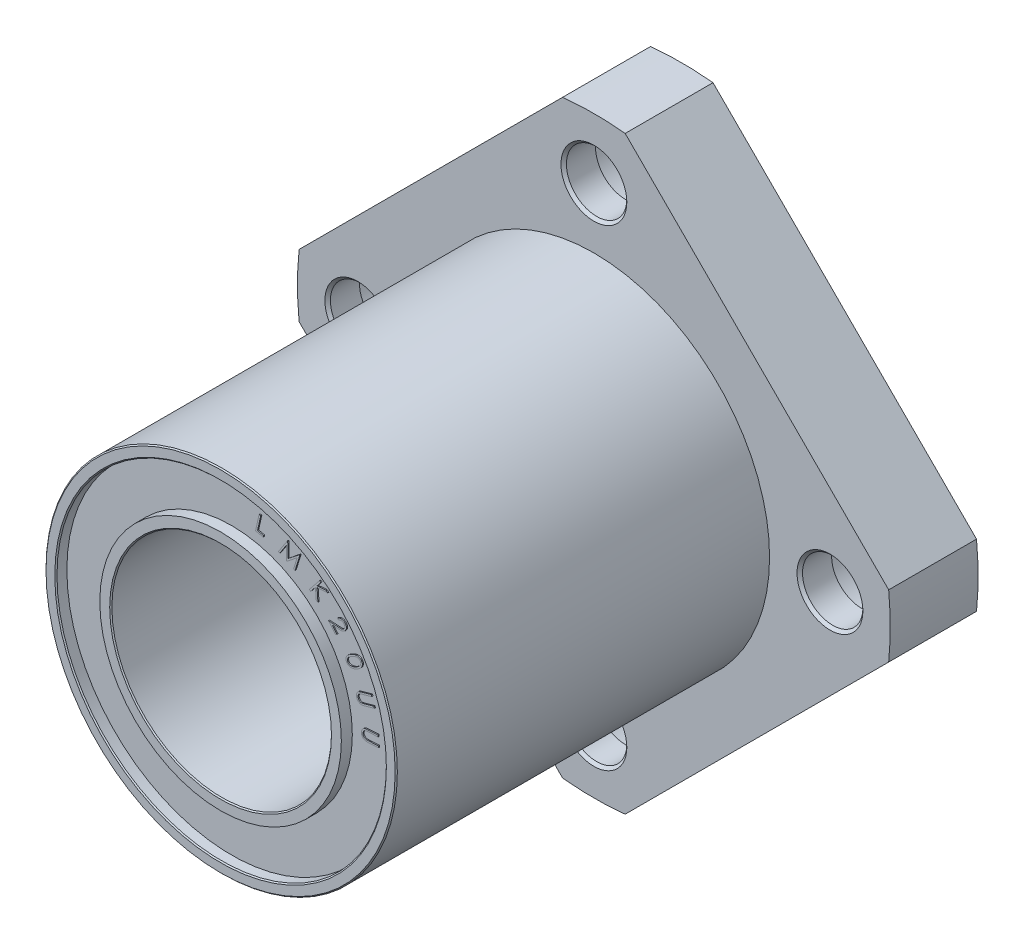
SolidWorks part; units mm, degrees
ref_plane "Front Plane" through (0, 0, 0) normal (0, 0, 1) x (1, 0, 0)
ref_plane "Top Plane" through (0, 0, 0) normal (0, 1, 0) x (1, 0, 0)
ref_plane "Right Plane" through (0, 0, 0) normal (1, 0, 0) x (0, 0, -1)
sketch "Sketch1" plane through (0, 0, 0) normal (0, 0, 1) x (1, 0, 0)
  line L1 (-2.8492, 26.8492) -> (-26.8492, 2.8492)
  line L2 (-26.8492, -2.8492) -> (-2.8492, -26.8492)
  line L3 (2.8492, -26.8492) -> (26.8492, -2.8492)
  line L4 (26.8492, 2.8492) -> (2.8492, 26.8492)
  arc A0 (-26.8492, 2.8492) -> (-26.8492, -2.8492) centre (0, 0) ccw
  circle A1 centre (0, 0) radius 21 construction
  arc A2 (-2.8492, -26.8492) -> (2.8492, -26.8492) centre (0, 0) ccw
  arc A3 (26.8492, -2.8492) -> (26.8492, 2.8492) centre (0, 0) ccw
  arc A4 (2.8492, 26.8492) -> (-2.8492, 26.8492) centre (0, 0) ccw
  dimension "D1" = 54
  dimension "D2" = 42
extrude "Boss-Extrude1" add sketch "Sketch1" along normal blind 8
sketch "Sketch2" plane through (0, 0, 8) normal (0, 0, 1) x (1, 0, 0)
  circle A0 centre (0, 0) radius 16
  dimension "D1" = 32
extrude "Boss-Extrude2" add sketch "Sketch2" along normal blind 34
sketch "Sketch3" plane through (0, 0, 0) normal (0, 0, -1) x (-1, 0, 0)
  circle A0 centre (0, 0) radius 21.5 construction
  circle A1 centre (0, 21.5) radius 4.5
  dimension "D1" = 43
  dimension "D2" = 9
extrude "Cut-Extrude1" cut sketch "Sketch3" against normal blind 5.1
sketch "Sketch4" plane through (0, 0, 5.1) normal (0, 0, -1) x (-1, 0, 0)
  circle A0 centre (0, 21.5) radius 2.75
  dimension "D1" = 5.5
extrude "Cut-Extrude2" cut sketch "Sketch4" against normal up to surface (2.9 mm away) up to face at (16, 0, 8)
chamfer "Chamfer1" distance 0.25 2 edges at (2.75, 21.5, 8) (-4.5, 21.5, 0)
pattern_circular "CirPattern1" count 4 over 360 about axis through (0, 0, 0) along (0, 0, 1) of "Chamfer1", "Cut-Extrude1", "Cut-Extrude2"
sketch "Sketch5" plane through (0, 0, 42) normal (0, 0, 1) x (1, 0, 0)
  circle A0 centre (0, 0) radius 10
  dimension "D1" = 20
extrude "Cut-Extrude3" cut sketch "Sketch5" against normal through all
sketch "Sketch6" plane through (0, 0, 42) normal (0, 0, 1) x (1, 0, 0)
  circle A0 centre (0, 0) radius 15
  circle A1 centre (0, 0) radius 11
  circle A2 centre (0, 0) radius 16 construction
  circle A3 centre (0, 0) radius 10 construction
  dimension "D1" = 1
  dimension "D2" = 1
extrude "Cut-Extrude4" cut sketch "Sketch6" against normal blind 1
sketch "Sketch7" plane through (0, 0, 0) normal (0, 0, -1) x (-1, 0, 0)
  circle A0 centre (0, 0) radius 11
  circle A1 centre (0, 0) radius 15
  circle A2 centre (0, 0) radius 15 construction
  circle A3 centre (0, 0) radius 11 construction
extrude "Cut-Extrude5" cut sketch "Sketch7" against normal blind 1
sketch "Sketch8" plane through (0, 0, 41) normal (0, 0, 1) x (1, 0, 0)
  circle A0 centre (0, 0) radius 12 construction
  circle A1 centre (0, 0) radius 11 construction
  text T0 "LMK20UU" font "Century Gothic" height 1.5
  dimension "D1" = 1
extrude "Boss-Extrude3" add sketch "Sketch8" along normal blind 0.1
chamfer "Chamfer2" distance 0.1 2 edges at (15, 0, 42) (16, 0, 42)
sketch "Sketch9" plane through (0, 0, 1) normal (0, 0, -1) x (-1, 0, 0)
  circle A0 centre (0, 0) radius 12 construction
  circle A1 centre (0, 0) radius 11 construction
  text T0 "LMK20UU" font "Century Gothic" height 1.5
  dimension "D1" = 1
extrude "Boss-Extrude4" add sketch "Sketch9" along normal blind 0.1
equation "\"d1\"= 54'2"
equation "\"D1@Sketch1\"=\"d1\""
equation "\"k\"= 42'1"
equation "\"D2@Sketch1\"=\"k\""
equation "\"h\"= 8'3"
equation "\"D1@Boss-Extrude1\"=\"h\""
equation "\"d\"= 32'5"
equation "\"D1@Sketch2\"=\"d\""
equation "\"l\"= 42'6"
equation "\"D1@Boss-Extrude2\"=\"l\"-\"h\""
equation "\"phi\"= 43'4"
equation "\"dd2\"= 9'7"
equation "\"hh\"= 5.1'8"
equation "\"dd1\"= 5.5'9"
equation "\"D1@Sketch3\"=\"phi\""
equation "\"D2@Sketch3\"=\"dd2\""
equation "\"D1@Cut-Extrude1\"=\"hh\""
equation "\"D1@Sketch4\"=\"dd1\""
equation "\"cha\"= 0.25'10"
equation "\"D1@Chamfer1\"=\"cha\""
equation "\"dr\"= 20'11"
equation "\"D1@Sketch5\"=\"dr\""
equation "\"vien\"= 1'12"
equation "\"D1@Sketch6\"=\"vien\""
equation "\"D2@Sketch6\"=\"vien\""
equation "\"D1@Cut-Extrude4\"=\"vien\""
equation "\"D1@Cut-Extrude5\"=\"vien\""
equation "\"D1@Sketch8\"=\"vien\""
equation "\"D1@Boss-Extrude3\"=\"vien\"/2"
equation "\"cha2\"= 0.2'13"
equation "\"D1@Sketch9\"=\"vien\""
